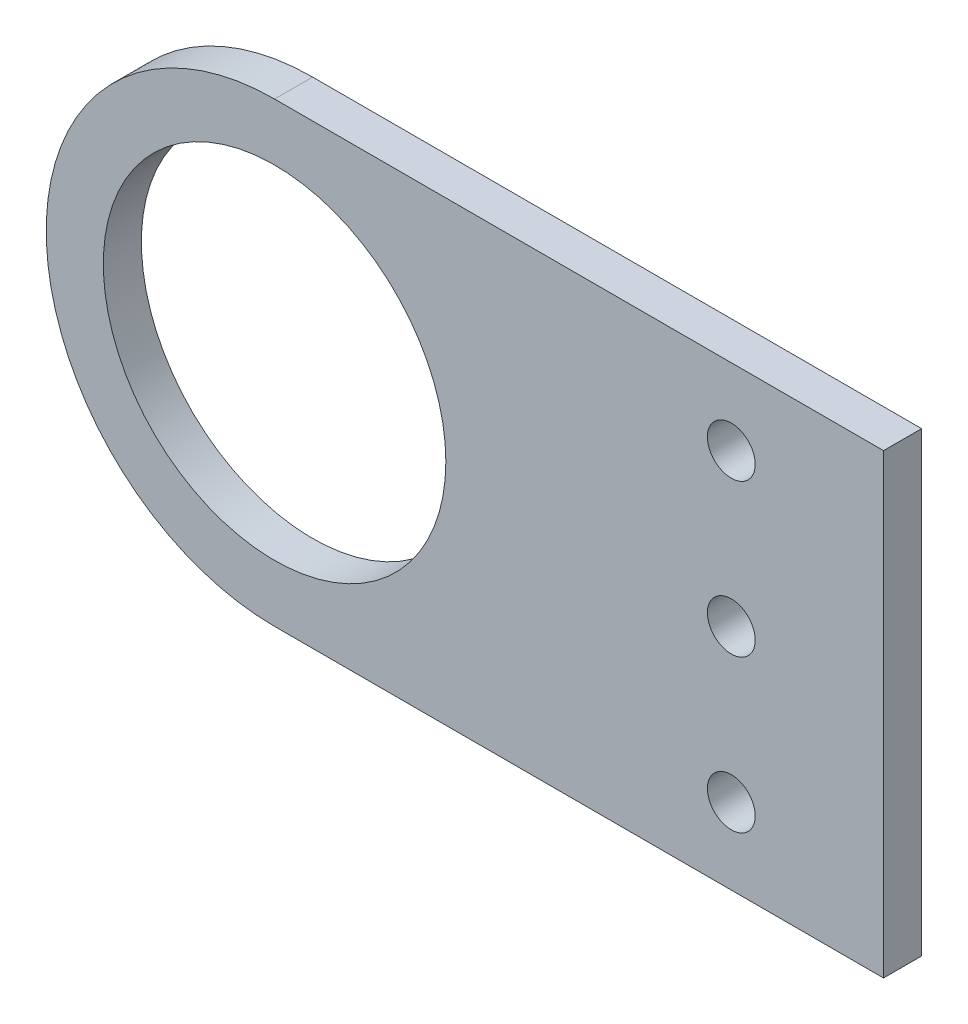
SolidWorks part; units mm, degrees
ref_plane "Front Plane" through (0, 0, 0) normal (0, 0, 1) x (1, 0, 0)
ref_plane "Top Plane" through (0, 0, 0) normal (0, 1, 0) x (1, 0, 0)
ref_plane "Right Plane" through (0, 0, 0) normal (1, 0, 0) x (0, 0, -1)
sketch "Sketch1" plane through (0, 0, 0) normal (0, 0, 1) x (1, 0, 0)
  line L0 (0, 19.05) -> (25.4, 19.05)
  line L1 (25.4, -19.05) -> (50.8, -19.05)
  line L3 (25.4, 19.05) -> (50.8, 19.05)
  line L4 (50.8, -19.05) -> (50.8, 19.05)
  line L5 (25.4, -19.05) -> (50.8, 19.05) construction
  line L6 (25.4, 19.05) -> (50.8, -19.05) construction
  line L7 (0, -19.05) -> (25.4, -19.05)
  circle A0 centre (0, 0) radius 14.2875
  circle A5 centre (38.1, -12.7) radius 1.9939
  circle A6 centre (38.1, 0) radius 1.9939
  circle A7 centre (38.1, 12.7) radius 1.9939
  arc A8 (0, 19.05) -> (0, -19.05) centre (0, 0) ccw
  point P14 (0, 0)
  dimension "D1" = 28.575
  dimension "D7" = 3.9878
  dimension "D2" = 25.4
  dimension "D3" = 38.1
  dimension "D6" = 38.1
  dimension "D8" = 12.7
  dimension "D9" = 3
extrude "Boss-Extrude1" add sketch "Sketch1" along normal blind 3.175
